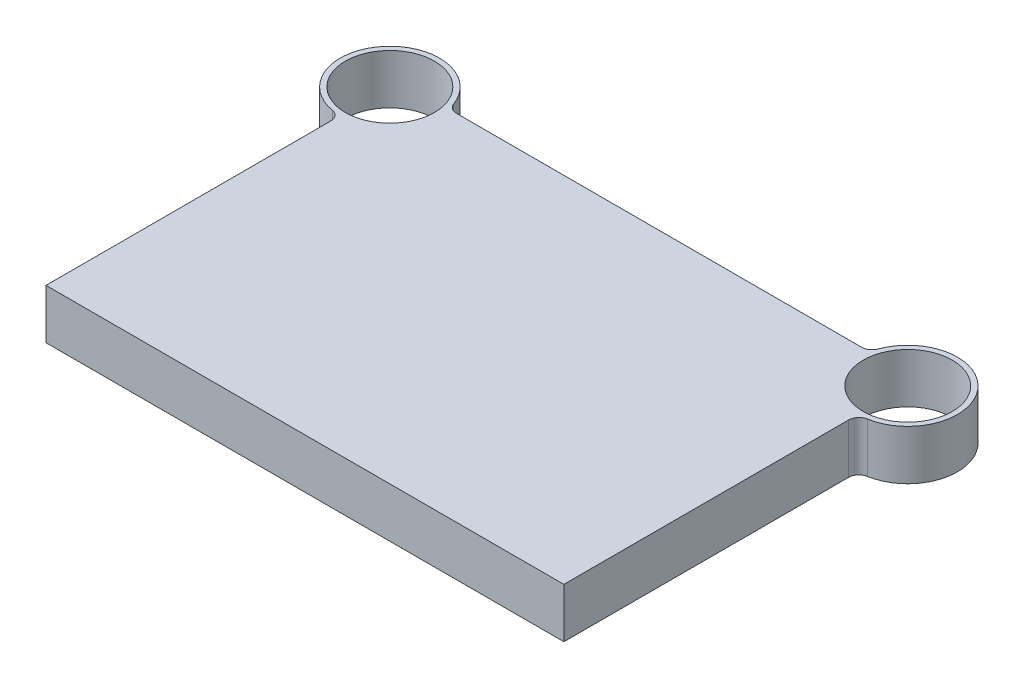
SolidWorks part; units mm, degrees
ref_plane "Front Plane" through (0, 0, 0) normal (0, 0, 1) x (1, 0, 0)
ref_plane "Top Plane" through (0, 0, 0) normal (0, 1, 0) x (1, 0, 0)
ref_plane "Right Plane" through (0, 0, 0) normal (1, 0, 0) x (0, 0, -1)
sketch "Sketch1" plane through (0, 0, 0) normal (0, 1, 0) x (1, 0, 0)
  line L0 (250, 0) -> (-250, 0)
  line L1 (-250, 0) -> (-250, 284)
  line L2 (0, 0) -> (0, 342) construction
  line L3 (203.0532, 342) -> (-203.0532, 342)
  line L4 (250, 0) -> (250, 284)
  arc A0 (-203.0532, 342) -> (-250, 284) centre (-250, 332) ccw
  circle A1 centre (-250, 332) radius 43
  circle A2 centre (250, 332) radius 43
  arc A3 (203.0532, 342) -> (250, 284) centre (250, 332) cw
  point P9 (-318.72, 268.4919)
  point P10 (-206.2071, 365.5495)
  dimension "D3" = 96
  dimension "D4" = 86
  dimension "D1" = 332
  dimension "D2" = 342
  dimension "D5" = 500
  dimension "D6" = 500
extrude "Boss-Extrude1" add sketch "Sketch1" along normal blind 48
fillet "Fillet1" radius 10 4 edges at (-250, 24, -284) (-203.0532, 24, -342) (203.0532, 24, -342) (250, 24, -284)
